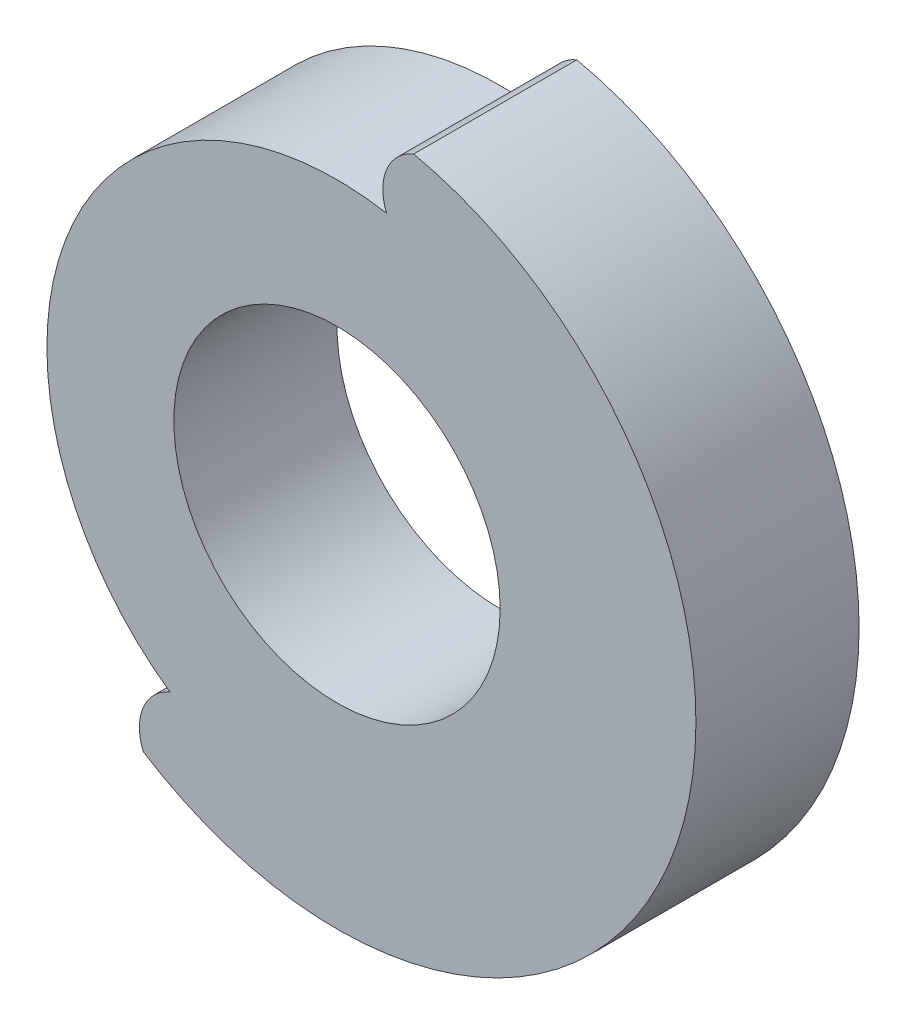
SolidWorks part; units mm, degrees
ref_plane "Front Plane" through (0, 0, 0) normal (0, 0, 1) x (1, 0, 0)
ref_plane "Top Plane" through (0, 0, 0) normal (0, 1, 0) x (1, 0, 0)
ref_plane "Right Plane" through (0, 0, 0) normal (1, 0, 0) x (0, 0, -1)
sketch "Sketch1" plane through (0, 0, 0) normal (0, 0, 1) x (1, 0, 0)
  circle A0 centre (0, 0) radius 6
  circle A1 centre (0, 0) radius 13.2
extrude "Boss-Extrude1" add sketch "Sketch1" along normal blind 6
sketch "Sketch2" plane through (0, 0, 6) normal (0, 0, 1) x (1, 0, 0)
  line L0 (0, 0) -> (0, 15.2) construction
  line L1 (-1.8199, 15.2) -> (0, 0) construction
  line L2 (1.8199, 15.2) -> (0, 0) construction
  arc A0 (-1.8199, 12) -> (1.8199, 12) centre (0, 0) cw
  arc A1 (-2.8199, 12.8953) -> (2.8199, 12.8953) centre (0, 0) cw
  arc A2 (-1.8199, 10.512) -> (1.8199, 10.512) centre (0, 0) cw
  arc A3 (-2.8199, 12.8953) -> (-1.8199, 10.512) centre (-3.5115, 11.2036) cw
  arc A4 (2.8199, 12.8953) -> (1.8199, 10.512) centre (3.5115, 11.2036) ccw
extrude "Cut-Extrude1" cut sketch "Sketch2" against normal through all contours A1 A4 A2 A3
pattern_circular "CirPattern2" count 10 every 15 about axis through (0, 0, 6) along (0, 0, 1) of "Cut-Extrude1"
